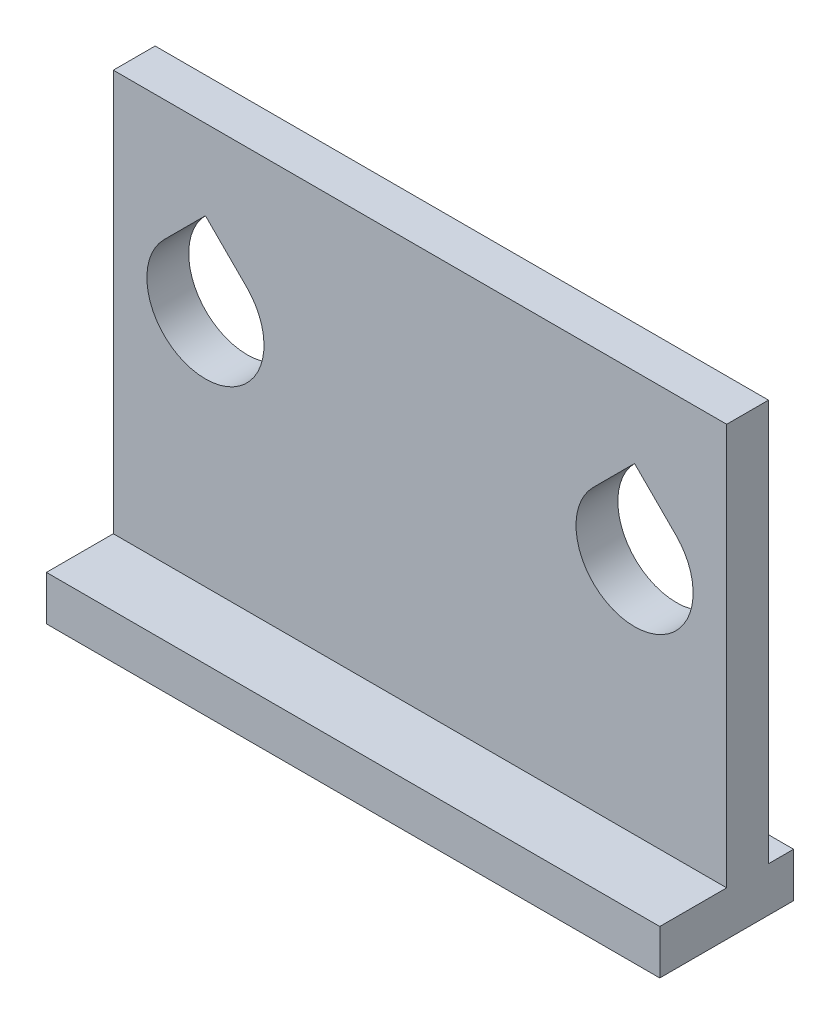
SolidWorks part; units mm, degrees
ref_plane "Front Plane" through (0, 0, 0) normal (0, 0, 1) x (1, 0, 0)
ref_plane "Top Plane" through (0, 0, 0) normal (0, 1, 0) x (1, 0, 0)
ref_plane "Right Plane" through (0, 0, 0) normal (1, 0, 0) x (0, 0, -1)
sketch "Sketch1" plane through (0, 0, 0) normal (0, 0, 1) x (1, 0, 0)
  line L0 (-38.481, 50.8) -> (38.481, 50.8) construction
  line L1 (-55, 0) -> (55, 0)
  line L2 (-55, 0) -> (-55, 80)
  line L3 (-55, 80) -> (55, 80)
  line L4 (55, 0) -> (55, 80)
  line L5 (38.481, 50.8) -> (0, 50.8)
  line L6 (0, 50.8) -> (0, 0) construction
  line L7 (-45.9056, 58.2246) -> (-38.481, 65.6492)
  line L8 (-38.481, 65.6492) -> (-31.0564, 58.2246)
  line L9 (31.0564, 58.2246) -> (38.481, 65.6492)
  line L10 (38.481, 65.6492) -> (45.9056, 58.2246)
  circle A0 centre (-38.481, 50.8) radius 10.5
  circle A1 centre (38.481, 50.8) radius 10.5
  point P4 (0, 0)
  dimension "D4" = 21
  dimension "D5" = 21
  dimension "D1" = 80
  dimension "D2" = 110
  dimension "D3" = 76.962
  dimension "D6" = 50.8
  dimension "D7" = 45
  dimension "D8" = 90
  dimension "D9" = 45
  dimension "D10" = 90
extrude "Boss-Extrude1" add sketch "Sketch1" along normal blind 7.5
sketch "Sketch3" plane through (0, 0, 7.5) normal (0, 0, 1) x (1, 0, 0)
  line L0 (55, 0) -> (55, 80) construction
  line L1 (-55, 0) -> (55, 0)
  line L2 (-55, 0) -> (-55, 8)
  line L3 (-55, 8) -> (55, 8)
  line L4 (55, 0) -> (55, 8)
extrude "Boss-Extrude2" add sketch "Sketch3" along normal blind 12 and the other way blind 12
equation "\"shaftDiam\" = 20mm"
equation "\"keyW\" = 8mm"
equation "\"keyL\" = 10mm"
equation "\"clearance\" = 1mm"
equation "\"handleShaftLen\" = 60mm"
equation "\"panelH\" = 80mm"
equation "\"panelW\" = 110mm"
equation "\"D1@Sketch1\"=\"panelH\""
equation "\"D2@Sketch1\"=\"panelW\""
equation "\"D3@Sketch1\"=3.03in"
equation "\"D4@Sketch1\" = \"shaftDiam\" + \"clearance\""
equation "\"D5@Sketch1\" = \"shaftDiam\" + \"clearance\""
equation "\"D6@Sketch1\"=4in/2"
equation "\"D1@Boss-Extrude1\"=\"handleShaftLen\"/8"
equation "\"D1@Sketch3\"=\"panelH\"/10"
equation "\"D1@Boss-Extrude2\"=\"handleShaftLen\"/5"
equation "\"D2@Boss-Extrude2\"=\"handleShaftLen\"/5"
